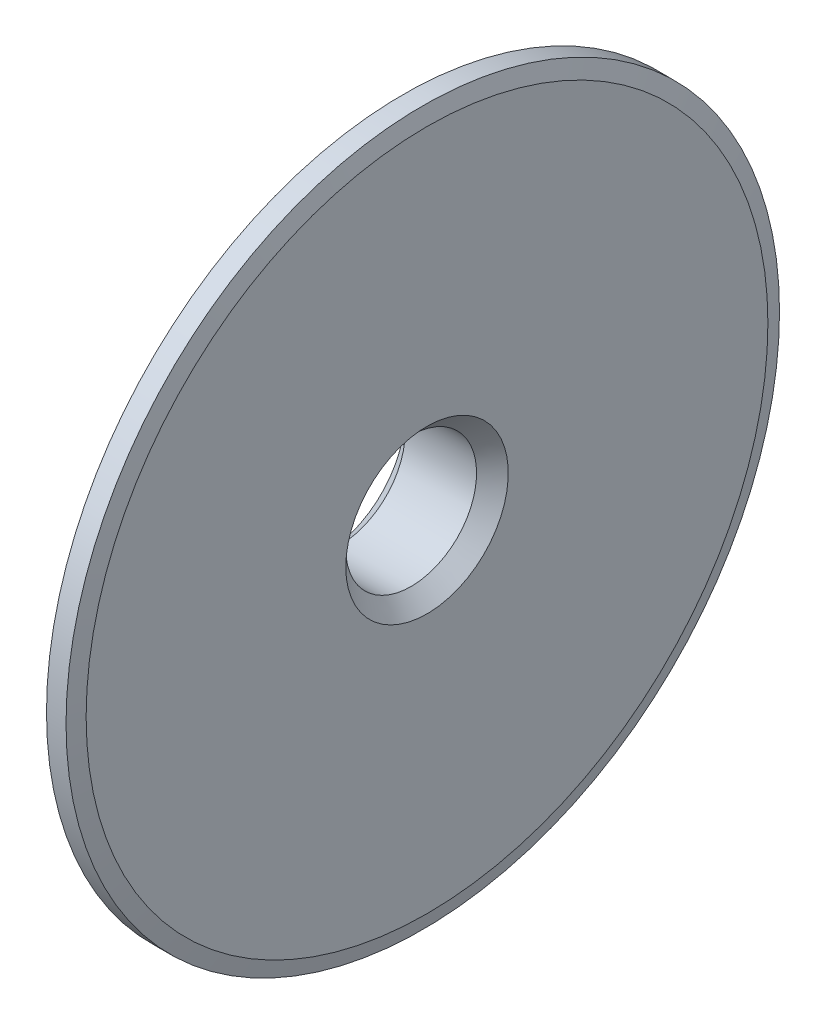
SolidWorks part; units mm, degrees
material "Сталь 40Х ГОСТ 4543-71"
ref_plane "Спереди (Плоскость XY)" through (0, 0, 0) normal (0, 0, 1) x (1, 0, 0)
ref_plane "Сверху (Плоскость XZ)" through (0, 0, 0) normal (0, 1, 0) x (1, 0, 0)
ref_plane "Справа (Плоскость ZY)" through (0, 0, 0) normal (1, 0, 0) x (0, 0, -1)
other "Configuration Table"
sketch "Эскиз1" plane through (0, 0, 0) normal (0, 0, 1) x (1, 0, 0)
  line L0 (0, 0) -> (129.3383, 0) construction
  line L1 (0, 8.25) -> (13, 8.25)
  line L2 (13, 8.25) -> (13, 43)
  line L3 (13, 43) -> (12.4641, 45)
  line L4 (12.4641, 45) -> (10, 45)
  line L5 (10, 45) -> (10, 32.5)
  line L6 (10, 32.5) -> (4, 32.5)
  line L7 (4, 32.5) -> (4, 30.5)
  line L8 (4, 30.5) -> (10, 30.5)
  line L9 (10, 30.5) -> (10, 12.5)
  line L10 (10, 12.5) -> (0, 12.5)
  line L11 (0, 12.5) -> (0, 8.25)
  line L12 (0, 0) -> (0, -53.2012) construction
  dimension "D1" = 16.5
  dimension "D2" = 61
  dimension "D3" = 10
  dimension "D4" = 3
  dimension "D5" = 65
  dimension "D6" = 25
  dimension "D7" = 10
  dimension "D8" = 6
  dimension "D9" = 90
  dimension "D10" = 15
  dimension "D11" = 0
  dimension "D12" = 86
revolve "Повернуть1" add sketch "Эскиз1" angle 360 about L0
cosmetic thread "Условное изображение резьбы1" parameters "D2"=18
chamfer "Фаска1" distance 2 angle 45 2 edges at (13, 0, 8.25) (0, 0, 8.25)
chamfer "Фаска3" distance 0.5 angle 45 3 edges at (0, 0, 12.5) (4, 0, 30.5) (4, 0, 32.5)
